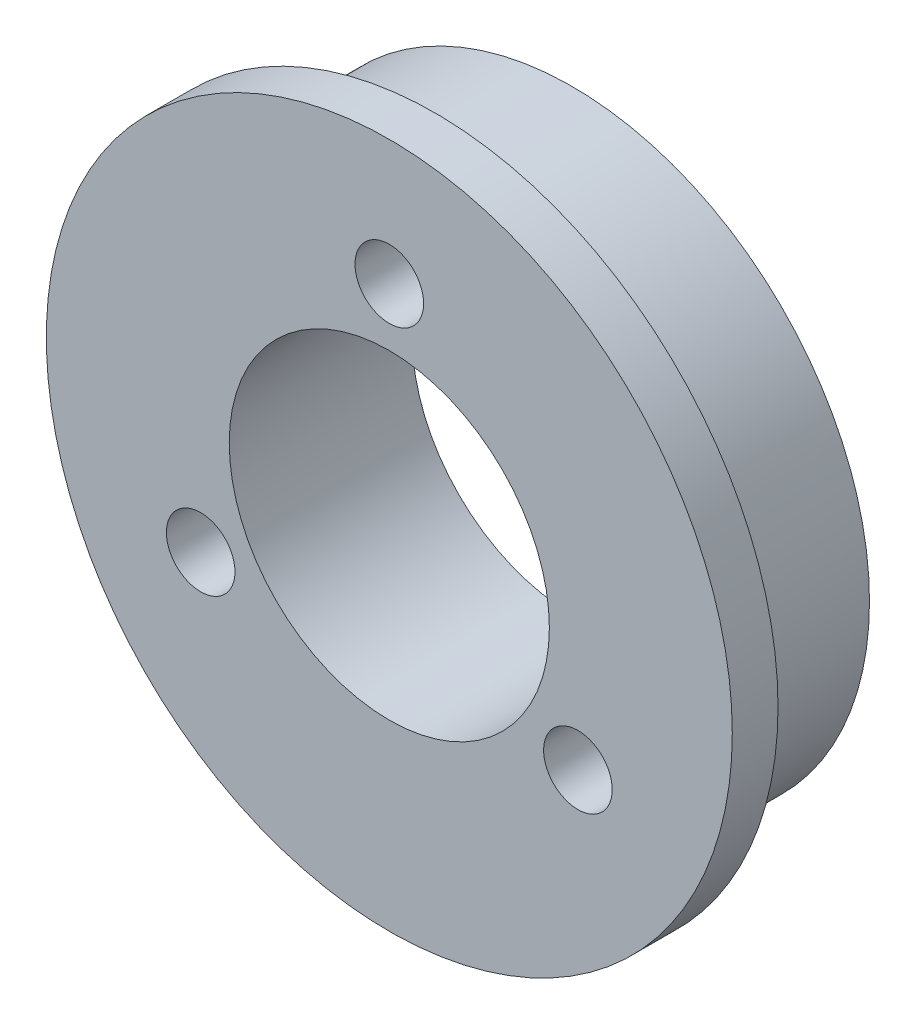
SolidWorks part; units mm, degrees
ref_plane "Front Plane" through (0, 0, 0) normal (0, 0, 1) x (1, 0, 0)
ref_plane "Top Plane" through (0, 0, 0) normal (0, 1, 0) x (1, 0, 0)
ref_plane "Right Plane" through (0, 0, 0) normal (1, 0, 0) x (0, 0, -1)
sketch "Sketch1" plane through (0, 0, 0) normal (0, 0, 1) x (1, 0, 0)
  circle A0 centre (0, 0) radius 7
  circle A1 centre (0, 0) radius 13
extrude "Boss-Extrude1" add sketch "Sketch1" along normal blind 6
sketch "Sketch2" plane through (0, 0, 6) normal (0, 0, 1) x (1, 0, 0)
  circle A0 centre (0, 0) radius 15
  circle A1 centre (0, 0) radius 7
extrude "Boss-Extrude2" add sketch "Sketch2" along normal blind 2
sketch "Sketch3" plane through (0, 0, 8) normal (0, 0, 1) x (1, 0, 0)
  circle A1 centre (0, 9.525) radius 1.5
  circle A2 centre (8.2489, -4.7625) radius 1.5
  circle A3 centre (-8.2489, -4.7625) radius 1.5
  point P11 (0, 0)
  dimension "D1" = 3
extrude "Cut-Extrude1" cut sketch "Sketch3" against normal blind 16
